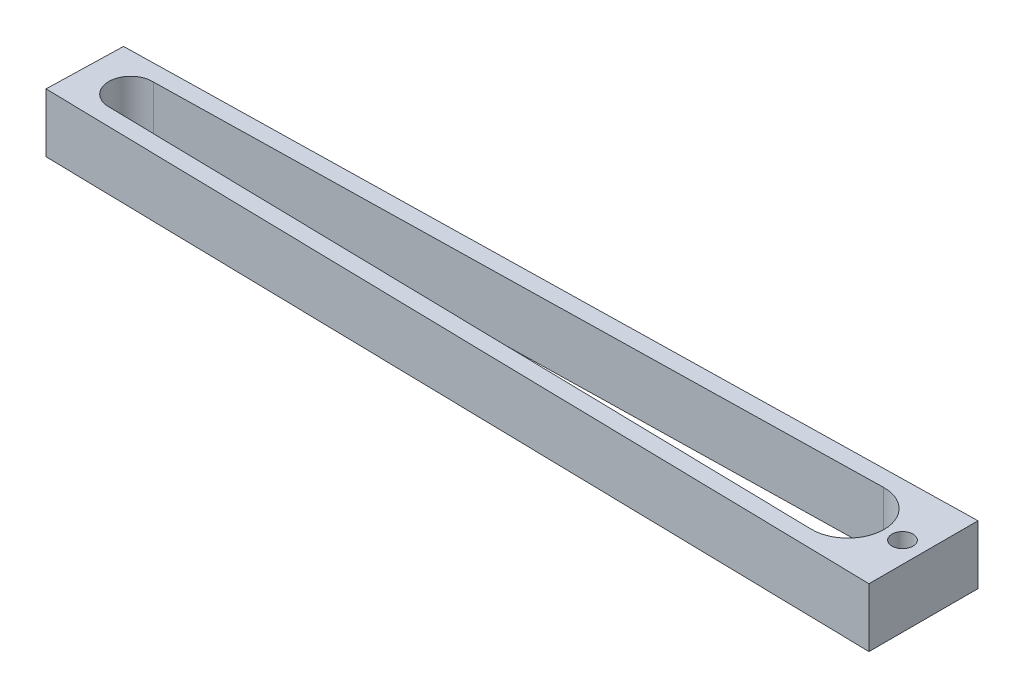
SolidWorks part; units mm, degrees
ref_plane "Front Plane" through (0, 0, 0) normal (0, 0, 1) x (1, 0, 0)
ref_plane "Top Plane" through (0, 0, 0) normal (0, 1, 0) x (1, 0, 0)
ref_plane "Right Plane" through (0, 0, 0) normal (1, 0, 0) x (0, 0, -1)
sketch "Sketch1" plane through (0, 0, 0) normal (0, 1, 0) x (1, 0, 0)
  line L29 (-90.0051, -41.9994) -> (-90.48, -59.9931)
  line L30 (-90.48, -59.9931) -> (109.52, -64.0568)
  line L31 (109.52, -64.0568) -> (109.52, -38.0977)
  line L32 (109.52, -38.0977) -> (-90.0051, -41.9994)
  line L33 (-90.2426, -50.9963) -> (109.52, -51.0772) construction
  line L34 (-58.6749, -44.2523) -> (-58.6777, -51.0091) construction
  line L48 (-49.8078, -41.272) -> (-49.8078, -41.2133)
  line L51 (-30.1907, -57.2108) -> (-30.3693, -57.2046)
  line L55 (91.3515, -42.4538) -> (-79.7182, -45.799)
  line L57 (91.3445, -59.686) -> (-79.4193, -56.217)
  line L58 (105.52, -42.1767) -> (-86.1073, -45.9239) construction
  line L59 (-86.1073, -45.9239) -> (-86.3752, -56.0757) construction
  line L60 (-86.3752, -56.0757) -> (105.52, -59.9747) construction
  line L61 (105.52, -59.9747) -> (105.52, -42.1767) construction
  circle A16 centre (104.52, -51.0752) radius 2.5
  arc A17 (78.0382, -58.2384) -> (78.1222, -58.2389) centre (78.1233, -51.0645) ccw
  arc A20 (78.169, -43.8903) -> (78.0833, -43.8902) centre (78.1233, -51.0645) ccw
  arc A22 (91.3445, -59.686) -> (91.3515, -42.4538) centre (91.52, -51.0699) ccw
  arc A24 (-30.3693, -57.2046) -> (-30.1907, -57.2108) centre (-30.0646, -51.0207) ccw
  arc A25 (-79.1122, -45.7872) -> (-79.4193, -56.217) centre (-79.3133, -51.0007) ccw
  point P1 (-48.8078, -41.272)
  point P4 (-48.8078, -60.7586)
  point P5 (105.52, -42.1767)
  point P7 (-86.1073, -45.9239)
  point P9 (-86.3752, -56.0757)
  point P10 (105.52, -59.9747)
  point P42 (-54.2997, -51.0083)
  point P45 (-88.7503, -50.9975)
  point P65 (94.6498, -46.8901)
  point P66 (-87.0785, -45.8643)
  point P67 (-87.396, -57.8974)
  point P68 (94.6498, -60.8578)
  point P70 (-49.8078, -60.7586)
  dimension "D8" = 5
  dimension "D9" = 5
  dimension "D1" = 200
  dimension "D2" = 4
  dimension "D5" = 18
extrude "Boss-Extrude1" add sketch "Sketch1" along normal blind 14
